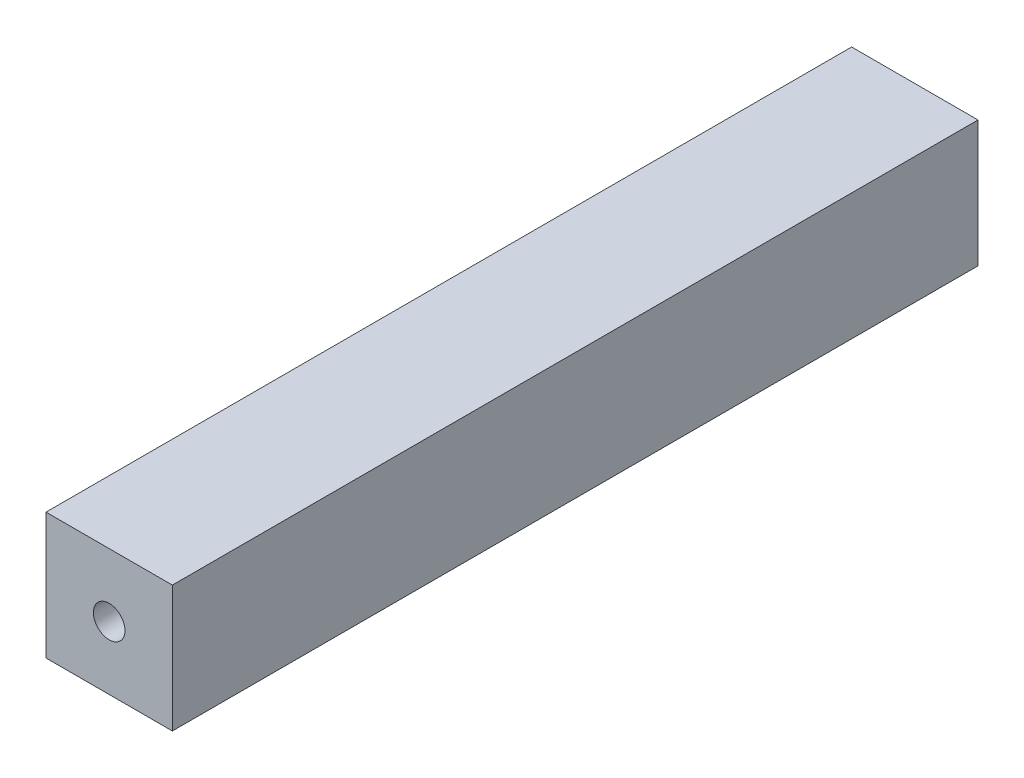
SolidWorks part; units mm, degrees
ref_plane "Front Plane" through (0, 0, 0) normal (0, 0, 1) x (1, 0, 0)
ref_plane "Top Plane" through (0, 0, 0) normal (0, 1, 0) x (1, 0, 0)
ref_plane "Right Plane" through (0, 0, 0) normal (1, 0, 0) x (0, 0, -1)
sketch "Sketch1" plane through (0, 0, 0) normal (0, 0, 1) x (1, 0, 0)
  line L8 (516, -189) -> (516, -229)
  line L9 (516, -229) -> (556, -229)
  line L10 (556, -229) -> (556, -189)
  line L11 (556, -189) -> (516, -189)
  circle A1 centre (536, -209) radius 5
extrude "Boss-Extrude1" add sketch "Sketch1" against normal blind 255
